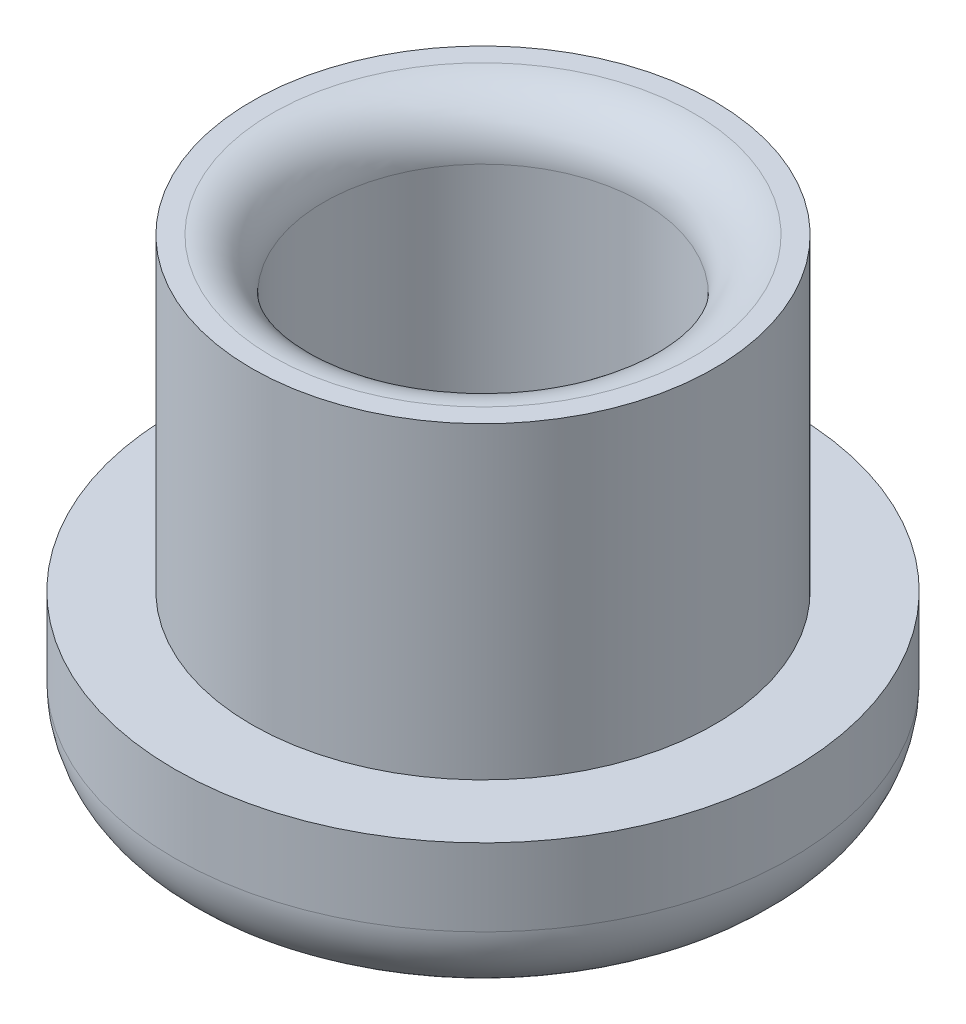
SolidWorks part; units mm, degrees
material "ABS"
ref_plane "正面" through (0, 0, 0) normal (0, 0, 1) x (1, 0, 0)
ref_plane "平面" through (0, 0, 0) normal (0, 1, 0) x (1, 0, 0)
ref_plane "右側面" through (0, 0, 0) normal (1, 0, 0) x (0, 0, -1)
sketch "ｽｹｯﾁ1" plane through (0, 0, 0) normal (0, 1, 0) x (1, 0, 0)
  circle A0 centre (0, 0) radius 6
  dimension "D1" = 12
extrude "ﾎﾞｽ - 押し出し1" add sketch "ｽｹｯﾁ1" along normal blind 3
sketch "ｽｹｯﾁ2" plane through (0, 3, 0) normal (0, 1, 0) x (1, 0, 0)
  circle A0 centre (0, 0) radius 4.5
  dimension "D1" = 9
extrude "押し出し-薄板1" add sketch "ｽｹｯﾁ2" along normal blind 6 thin thin type one direction reverse wall 1.4
fillet "ﾌｨﾚｯﾄ1" radius 1 2 edges at (3.1, 9, 0) (0, 3, 3.1)
fillet "ﾌｨﾚｯﾄ2" radius 1.5 1 edges at (0, 0, 6)
